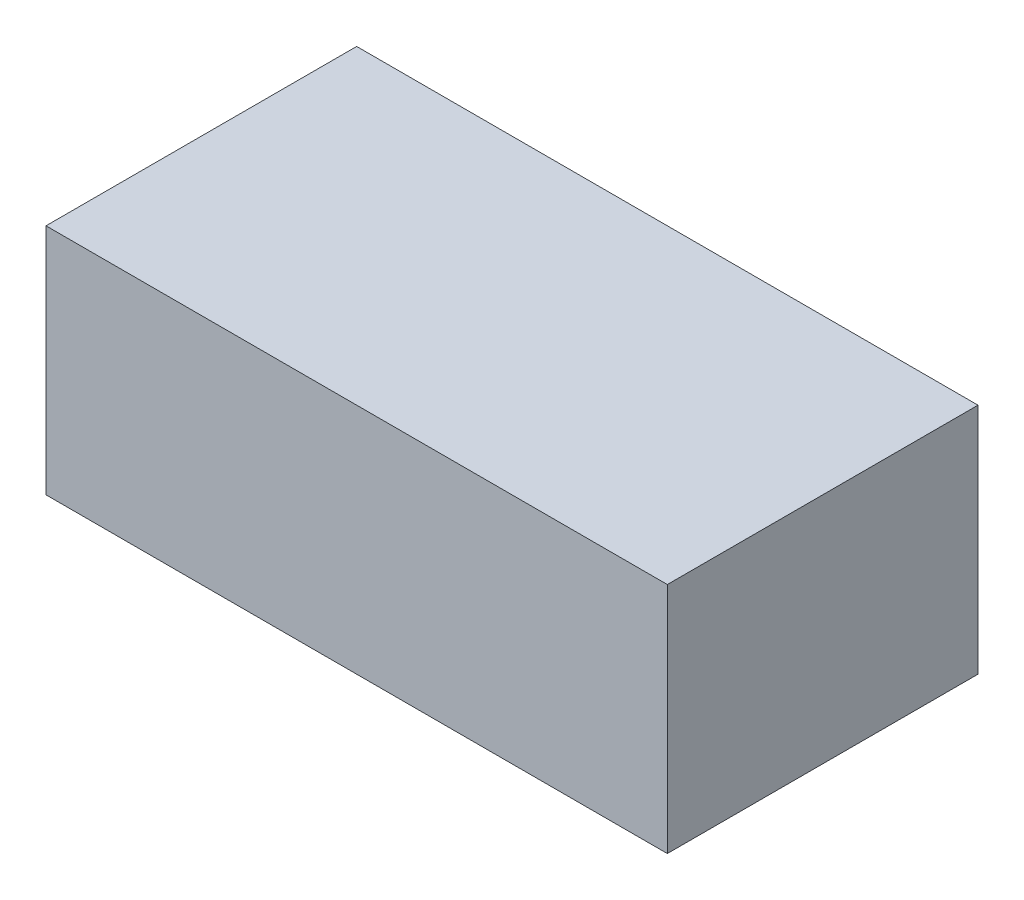
SolidWorks part; units mm, degrees
ref_plane "Спереди" through (0, 0, 0) normal (0, 0, 1) x (1, 0, 0)
ref_plane "Сверху" through (0, 0, 0) normal (0, 1, 0) x (1, 0, 0)
ref_plane "Справа" through (0, 0, 0) normal (1, 0, 0) x (0, 0, -1)
sketch "Эскиз1" plane through (0, 0, 0) normal (0, 1, 0) x (1, 0, 0)
  line L1 (-80, 40) -> (80, 40)
  line L2 (-80, 40) -> (-80, -40)
  line L3 (-80, -40) -> (80, -40)
  line L4 (80, 40) -> (80, -40)
  line L5 (-80, 40) -> (80, -40) construction
  line L6 (-80, -40) -> (80, 40) construction
  point P0 (0, 0)
extrude "Бобышка-Вытянуть1" add sketch "Эскиз1" along normal blind 60
